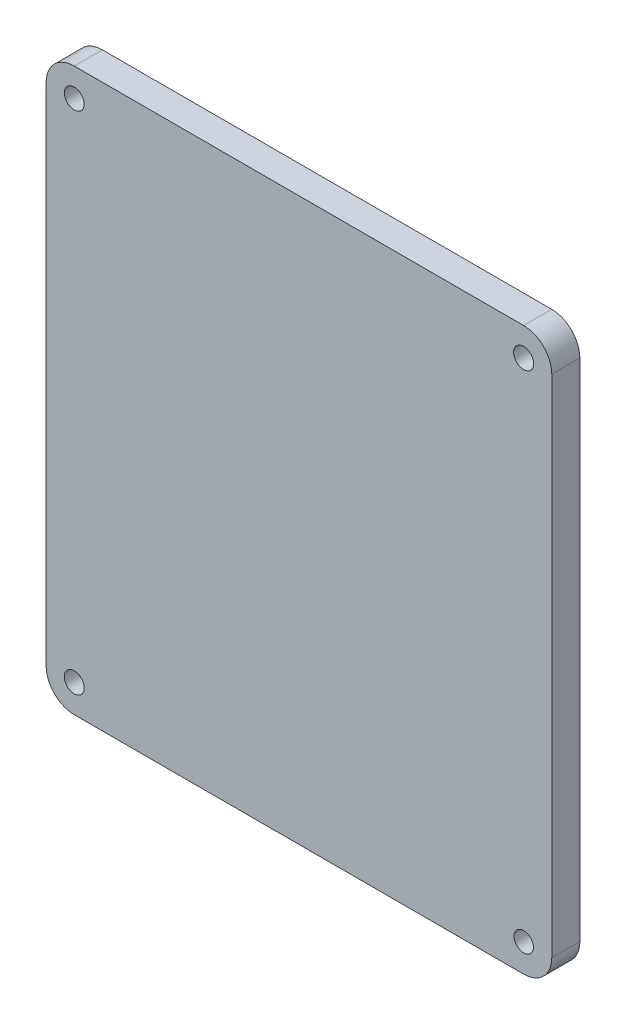
SolidWorks part; units mm, degrees
ref_plane "Front Plane" through (0, 0, 0) normal (0, 0, 1) x (1, 0, 0)
ref_plane "Top Plane" through (0, 0, 0) normal (0, 1, 0) x (1, 0, 0)
ref_plane "Right Plane" through (0, 0, 0) normal (1, 0, 0) x (0, 0, -1)
sketch "Sketch1" plane through (0, 0, 0) normal (0, 0, 1) x (1, 0, 0)
  line L1 (93.2182, -42.8306) -> (-66.7818, -42.8306)
  line L2 (103.2182, -32.8306) -> (103.2182, 147.1694)
  line L3 (93.2182, 157.1694) -> (-66.7818, 157.1694)
  line L4 (-76.7818, -32.8306) -> (-76.7818, 147.1694)
  arc A0 (93.2182, -42.8306) -> (103.2182, -32.8306) centre (93.2182, -32.8306) ccw
  arc A1 (-66.7818, -42.8306) -> (-76.7818, -32.8306) centre (-66.7818, -32.8306) cw
  arc A2 (103.2182, 147.1694) -> (93.2182, 157.1694) centre (93.2182, 147.1694) ccw
  arc A3 (-66.7818, 157.1694) -> (-76.7818, 147.1694) centre (-66.7818, 147.1694) ccw
  dimension "D1" = 10
extrude "Boss-Extrude1" add sketch "Sketch1" along normal blind 10
sketch "Sketch3" plane through (0, 0, 10) normal (0, 0, 1) x (1, 0, 0)
  circle A0 centre (-66.7818, -32.8306) radius 3.5576
  circle A1 centre (93.2182, -32.8306) radius 3.4501
  circle A2 centre (93.2182, 147.1694) radius 3.5758
  circle A3 centre (-66.7818, 147.1694) radius 3.5318
extrude "Cut-Extrude3" cut sketch "Sketch3" against normal blind 10
